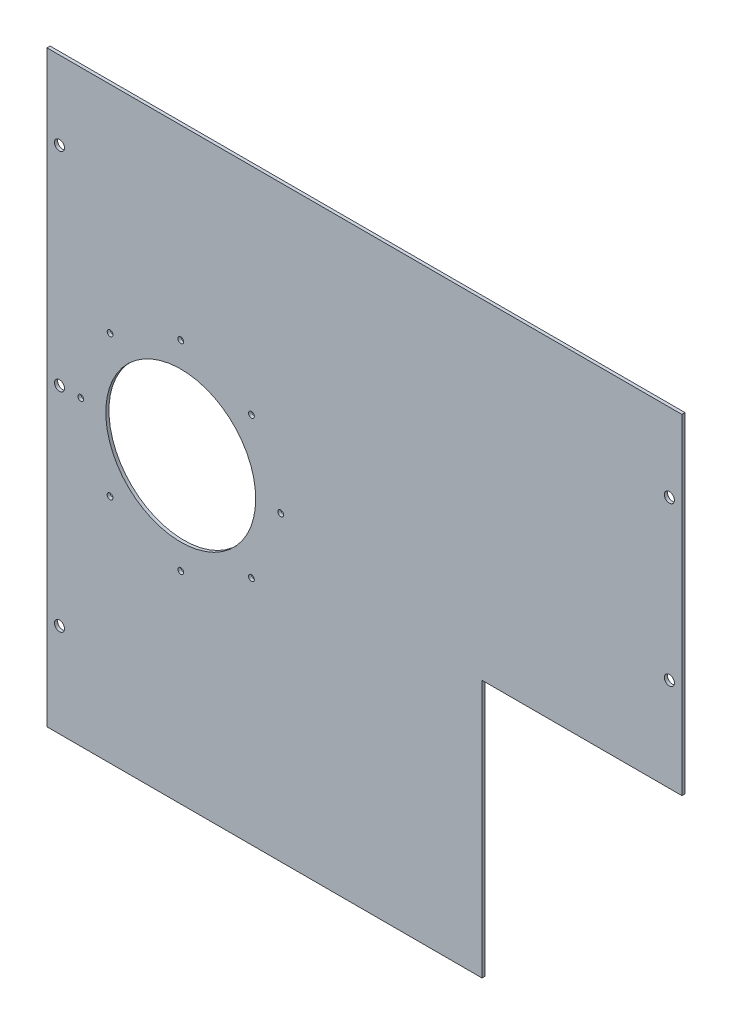
SolidWorks part; units mm, degrees
material "6061-T6 (SS)"
ref_plane "Front Plane" through (0, 0, 0) normal (0, 0, 1) x (1, 0, 0)
ref_plane "Top Plane" through (0, 0, 0) normal (0, 1, 0) x (1, 0, 0)
ref_plane "Right Plane" through (0, 0, 0) normal (1, 0, 0) x (0, 0, -1)
sketch "Sketch1" plane through (0, 0, 0) normal (0, 0, 1) x (1, 0, 0)
  line L0 (161.3627, -22.3467) -> (59.7625, -22.3467)
  line L1 (-161.3627, 145.4859) -> (161.3627, 145.4859)
  line L2 (-161.3627, 145.4859) -> (-161.3627, -153.4107)
  line L3 (-161.3627, -153.4107) -> (59.7625, -153.4107)
  line L4 (161.3627, 145.4859) -> (161.3627, -22.3467)
  line L5 (59.7625, -22.3467) -> (59.7625, -153.4107)
  line L6 (0, 0) -> (0, 57.0615) construction
  line L7 (59.7625, -153.4107) -> (161.3627, -153.4107) construction
  line L8 (161.3627, -22.3467) -> (161.3627, -153.4107) construction
  line L9 (0, 0) -> (-41.9055, 0) construction
  point P11 (0, 145.4859)
  dimension "D1" = 298.8966
  dimension "D2" = 322.7254
  dimension "D3" = 131.064
  dimension "D4" = 101.6002
  dimension "D5" = 153.4107
extrude "Boss-Extrude1" add sketch "Sketch1" along normal blind 1.6002
sketch "Sketch2" plane through (0, 0, 1.6002) normal (0, 0, 1) x (1, 0, 0)
  line L0 (0, 0) -> (39.3414, 0) construction
  line L1 (-161.3627, 145.4859) -> (-161.3627, -153.4107) construction
  circle A0 centre (-93.3627, 0) radius 38.1
  dimension "D1" = 76.2
  dimension "D2" = 68
extrude "Cut-Extrude1" cut sketch "Sketch2" against normal through all
sketch "Sketch10" plane through (0, 0, 1.6002) normal (0, 0, 1) x (1, 0, 0)
  line L0 (-93.3627, 0) -> (-93.3627, 50.8) construction
  dimension "D1" = 50.8
hole_wizard "#4 Clearance Hole1" positions "Sketch12" profile "Sketch11" hole size "#4" standard "ANSI Inch"
sketch "Sketch12" plane through (0, 0, 1.6002) normal (0, 0, 1) x (1, 0, 0)
  point P0 (-93.3627, 50.8)
sketch "Sketch11" plane through (-93.3627, 50.8, 1.6002) normal (1, 0, 0) x (0, -1, 0)
  line L0 (0, 0) -> (0, 173.8552)
  line L1 (0, 173.8552) -> (1.4732, 172.97)
  line L2 (1.4732, 172.97) -> (1.4732, 0)
  line L5 (1.4732, 0) -> (0, 0)
  line L10 (0, 173.8552) -> (-1.4732, 172.97) construction
  line L11 (0, -6.35) -> (0, 107.95) construction
  dimension "Hole Dia." = 2.9464
  dimension "Hole Depth" = 172.97
  dimension "Drill Angle" = 118
pattern_circular "CirPattern1" count 8 over 360 about axis through (-93.3627, 0, 0) along (0, 0, 1) of "#4 Clearance Hole1"
hole_wizard "#10 Clearance Hole1" positions "Sketch14" profile "Sketch13" hole size "#10" standard "ANSI Inch"
sketch "Sketch14" plane through (0, 0, 1.6002) normal (0, 0, 1) x (1, 0, 0)
  line L0 (0, 0) -> (60.1505, 0) construction
  line L1 (0, 0) -> (0, 66.6498) construction
  line L2 (-155, 105.7857) -> (-155, 75.892) construction
  line L3 (155, 95.0853) -> (155, 66.6498) construction
  point P0 (-155, 105.7857)
  point P15 (155, 105.7857)
  point P20 (-155, -105.7857)
  point P21 (155, 25.2785)
  point P24 (-155, 0)
  dimension "D1" = 155
  dimension "D2" = 105.7857
  dimension "D3" = 25.2785
sketch "Sketch13" plane through (-155, 105.7857, 1.6002) normal (1, 0, 0) x (0, -1, 0)
  line L0 (0, 0) -> (0, 131.0638)
  line L1 (0, 131.0638) -> (2.5527, 129.53)
  line L2 (2.5527, 129.53) -> (2.5527, 0)
  line L5 (2.5527, 0) -> (0, 0)
  line L10 (0, 131.0638) -> (-2.5527, 129.53) construction
  line L11 (0, -6.35) -> (0, 107.95) construction
  dimension "Hole Dia." = 5.1054
  dimension "Hole Depth" = 129.53
  dimension "Drill Angle" = 118
